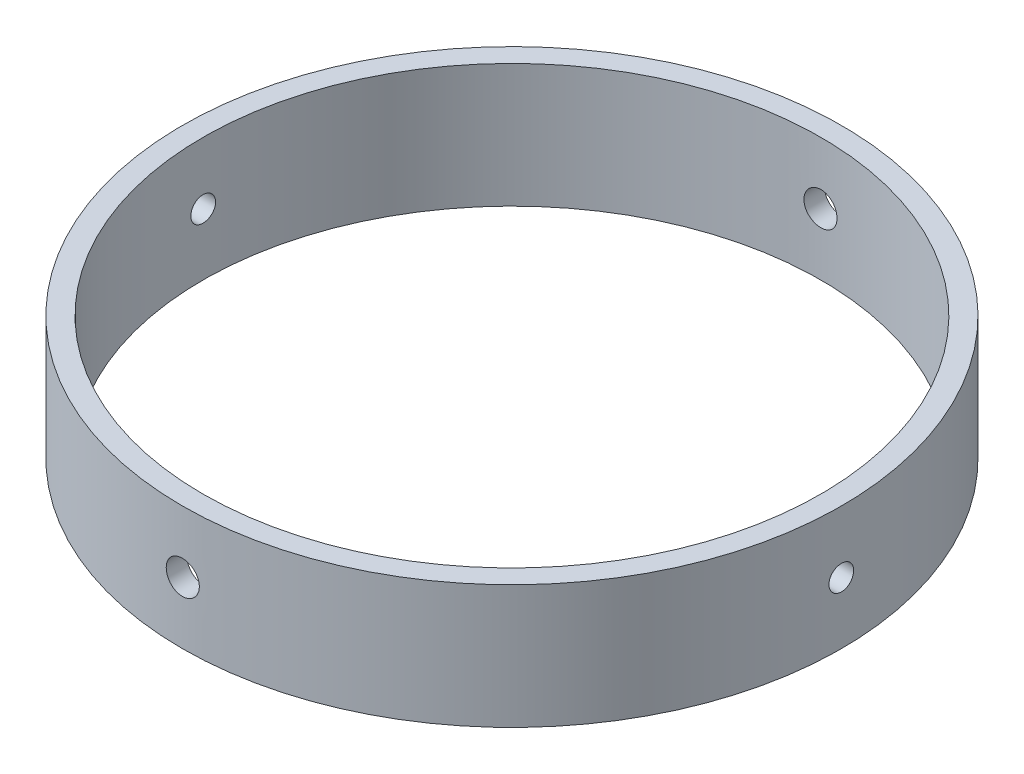
SolidWorks part; units mm, degrees
ref_plane "Front Plane" through (0, 0, 0) normal (0, 0, 1) x (1, 0, 0)
ref_plane "Top Plane" through (0, 0, 0) normal (0, 1, 0) x (1, 0, 0)
ref_plane "Right Plane" through (0, 0, 0) normal (1, 0, 0) x (0, 0, -1)
sketch "Sketch1" plane through (0, 0, 0) normal (0, 1, 0) x (1, 0, 0)
  circle A0 centre (0, 0) radius 50.8
  circle A1 centre (0, 0) radius 47.625
  dimension "D1" = 101.6
  dimension "D2" = 95.25
extrude "Boss-Extrude1" add sketch "Sketch1" along normal blind 19.05
ref_plane "Plane1" through (0, 0, 31.75) normal (0, 0, 1) x (1, 0, 0)
ref_plane "Plane2" through (0, 0, -31.75) normal (0, 0, 1) x (1, 0, 0)
sketch "Sketch3" plane through (0, 0, 31.75) normal (0, 0, 1) x (1, 0, 0)
  line L0 (47.625, 19.05) -> (-47.625, 19.05) construction
  circle A0 centre (0, 9.525) radius 2.7224
  dimension "D1" = 9.525
hole_wizard "Tap Drill for 1/4-20 Tap1" positions "Sketch4" profile "Sketch5" hole size "1/4-20" standard "ANSI Inch"
sketch "Sketch4" plane through (0, 0, 31.75) normal (0, 0, 1) x (1, 0, 0)
  point P0 (0, 9.525)
sketch "Sketch5" plane through (0, 9.525, 31.75) normal (1, 0, 0) x (0, -1, 0)
  line L0 (0, 0) -> (0, 82.55)
  line L1 (0, 82.55) -> (2.5527, 82.55)
  line L2 (2.5527, 82.55) -> (2.5527, 0)
  line L5 (2.5527, 0) -> (0, 0)
  line L11 (0, -6.35) -> (0, 107.95) construction
  dimension "Thru Hole Dia." = 5.1054
  dimension "Thru Hole Depth" = 82.55
sketch "Sketch7" plane through (0, 0, -31.75) normal (0, 0, 1) x (1, 0, 0)
  line L0 (50.8, 19.05) -> (-50.8, 19.05) construction
  circle A0 centre (0, 9.525) radius 3.5632
  dimension "D1" = 9.525
hole_wizard "Tap Drill for 1/4-20 Tap2" positions "Sketch8" profile "Sketch9" hole size "1/4-20" standard "ANSI Inch" end condition up to next
sketch "Sketch8" plane through (0, 0, -31.75) normal (0, 0, 1) x (1, 0, 0)
  point P0 (0, 9.525)
sketch "Sketch9" plane through (0, 9.525, -31.75) normal (1, 0, 0) x (0, 1, 0)
  line L0 (0, 0) -> (0, 82.55)
  line L1 (0, 82.55) -> (2.5527, 82.55)
  line L2 (2.5527, 82.55) -> (2.5527, 0)
  line L5 (2.5527, 0) -> (0, 0)
  line L11 (0, -6.35) -> (0, 107.95) construction
  dimension "Thru Hole Dia." = 5.1054
  dimension "Thru Hole Depth" = 82.55
ref_plane "Plane3" through (31.75, 0, 0) normal (1, 0, 0) x (0, 0, -1)
ref_plane "Plane4" through (-31.75, 0, 0) normal (1, 0, 0) x (0, 0, -1)
sketch "Sketch10" plane through (-31.75, 0, 0) normal (1, 0, 0) x (0, 0, -1)
  circle A0 centre (0, 9.4879) radius 1.905
  dimension "D1" = 3.81
extrude "Cut-Extrude3" cut sketch "Sketch10" against normal through all and the other way through all
sketch3d "3DSketch1"
  point P0 (46.2948, 8.9339, 20.9149)
